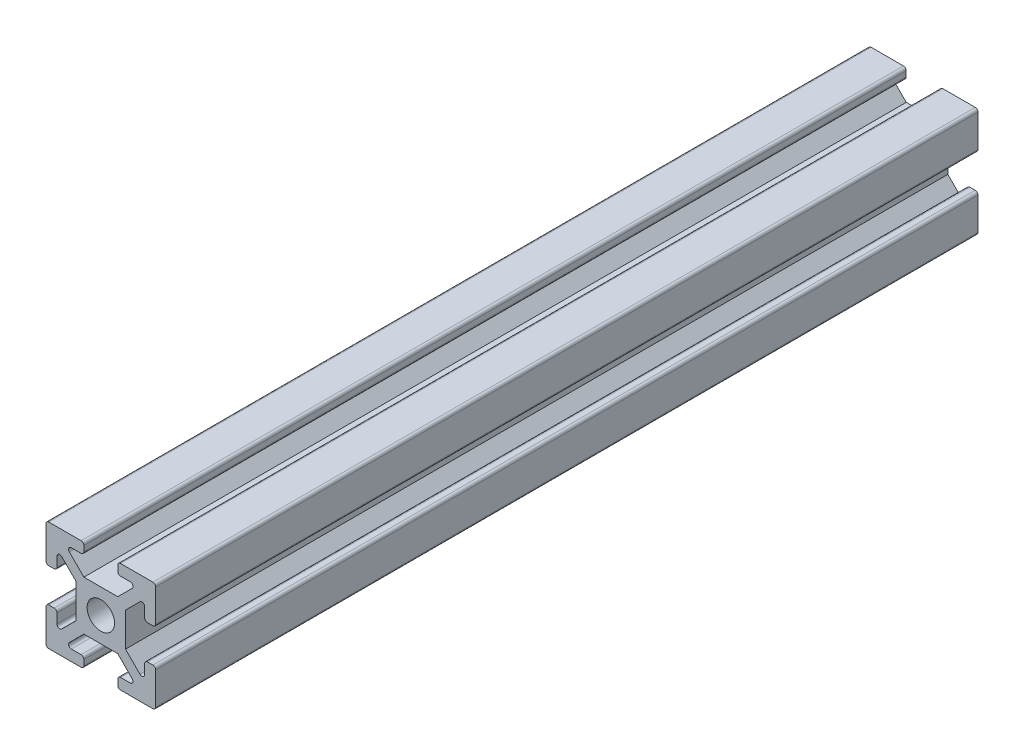
SolidWorks part; units mm, degrees
material "3.2381 (EN-AW-43000)"
ref_plane "Ebene vorne" through (0, 0, 0) normal (0, 0, 1) x (1, 0, 0)
ref_plane "Ebene oben" through (0, 0, 0) normal (0, 1, 0) x (1, 0, 0)
ref_plane "Ebene rechts" through (0, 0, 0) normal (1, 0, 0) x (0, 0, -1)
sketch "Skizze1" plane through (0, 0, 0) normal (0, 0, 1) x (1, 0, 0)
  line L0 (-0.7071, 0.7071) -> (6.5858, 8)
  line L1 (-10, -10) -> (10, -10) construction
  line L2 (-10, -10) -> (-10, 10) construction
  line L3 (-10, 10) -> (10, 10) construction
  line L4 (10, -10) -> (10, 10) construction
  line L5 (-10, -10) -> (10, 10) construction
  line L6 (-10, 10) -> (10, -10) construction
  line L7 (6.5858, 8) -> (3.1, 8)
  line L8 (3.1, 8) -> (3.1, 10)
  line L9 (3.1, 10) -> (10, 10)
  line L10 (10, 10) -> (10, 3.1)
  line L11 (10, 3.1) -> (8, 3.1)
  line L12 (8, 3.1) -> (8, 6.5858)
  line L13 (8, 6.5858) -> (0.7071, -0.7071)
  line L14 (0.7071, -0.7071) -> (-0.7071, 0.7071)
  point P0 (0, 0)
  point P14 (0, 0)
  dimension "D1" = 2
  dimension "D2" = 3.1
  dimension "D3" = 20
extrude "Aufsatz-Linear austragen1" add sketch "Skizze1" along normal blind 150
sketch "Skizze2" plane through (0, 0, 0) normal (-0.7071, -0.7071, 0) x (0, 0, 1)
  line L0 (0, 0) -> (150, 0) construction
  line L1 (150, 1) -> (150, -1) construction
fillet "Verrundung1" radius 0.5 7 edges at (6.5858, 8, 75) (8, 6.5858, 75) (10, 10, 75) (3.1, 8, 75) (8, 3.1, 75) (10, 3.1, 75) (3.1, 10, 75)
pattern_circular "Kreismuster1" count 4 over 360 about axis through (0, 0, 0) along (0, 0, 1) of "Aufsatz-Linear austragen1", "Verrundung1"
sketch "Skizze3" plane through (0, 0, 150) normal (0, 0, 1) x (1, 0, 0)
  line L1 (-4.5, -4.5) -> (4.5, -4.5)
  line L2 (-4.5, -4.5) -> (-4.5, 4.5)
  line L3 (-4.5, 4.5) -> (4.5, 4.5)
  line L4 (4.5, -4.5) -> (4.5, 4.5)
  line L5 (-4.5, -4.5) -> (4.5, 4.5) construction
  line L6 (-4.5, 4.5) -> (4.5, -4.5) construction
  point P0 (0, 0)
  dimension "D1" = 9
extrude "Aufsatz-Linear austragen2" add sketch "Skizze3" against normal up to surface (150 mm away) up to face at (0, 0, 0)
sketch "Skizze4" plane through (0, 0, 150) normal (0, 0, 1) x (1, 0, 0)
  circle A0 centre (0, 0) radius 2.5
  dimension "D1" = 5
extrude "Schnitt-Linear austragen1" cut sketch "Skizze4" against normal through all
